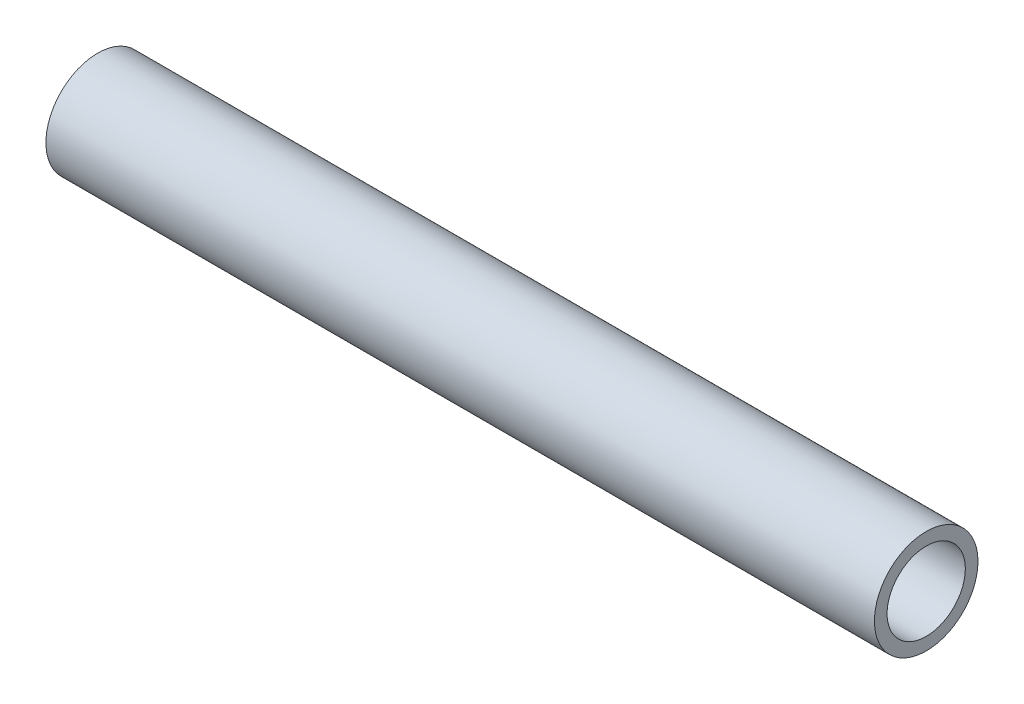
SolidWorks part; units mm, degrees
ref_plane "Front Plane" through (0, 0, 0) normal (0, 0, 1) x (1, 0, 0)
ref_plane "Top Plane" through (0, 0, 0) normal (0, 1, 0) x (1, 0, 0)
ref_plane "Right Plane" through (0, 0, 0) normal (1, 0, 0) x (0, 0, -1)
sketch "Sketch1" plane through (0, 0, 0) normal (1, 0, 0) x (0, 0, -1)
  circle A0 centre (0, 0) radius 28.575
  circle A1 centre (0, 0) radius 21.59
  dimension "D1" = 57.15
  dimension "D2" = 43.18
extrude "Boss-Extrude1" add sketch "Sketch1" along normal mid plane 457.2
